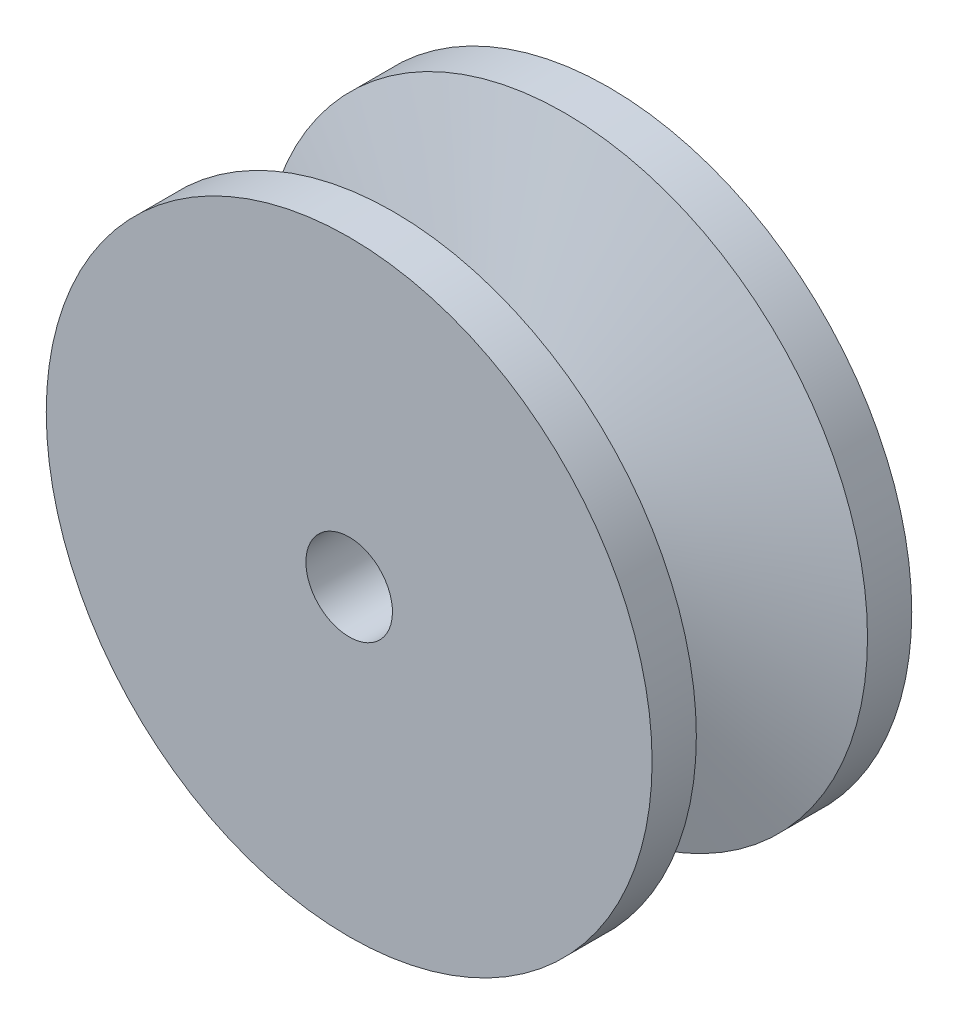
SolidWorks part; units mm, degrees
ref_plane "Front Plane" through (0, 0, 0) normal (0, 0, 1) x (1, 0, 0)
ref_plane "Top Plane" through (0, 0, 0) normal (0, 1, 0) x (1, 0, 0)
ref_plane "Right Plane" through (0, 0, 0) normal (1, 0, 0) x (0, 0, -1)
sketch "Sketch1" plane through (0, 0, 0) normal (1, 0, 0) x (0, 0, -1)
  line L0 (-9.525, 0) -> (9.525, 0) construction
  line L1 (-6.2793, 22.225) -> (6.2793, 22.225) construction
  line L2 (6.2793, 22.225) -> (9.525, 22.225)
  line L5 (-9.525, 22.225) -> (6.2793, 22.225) construction
  line L13 (-6.2793, 22.225) -> (-2.4742, 9.779)
  line L14 (-2.4742, 9.779) -> (2.4742, 9.779)
  line L15 (2.4742, 9.779) -> (6.2793, 22.225)
  line L16 (9.525, 3.175) -> (-9.525, 3.175) construction
  line L17 (0, 22.225) -> (0, 0) construction
  line L18 (-6.2793, 22.225) -> (-9.525, 22.225)
  line L22 (5.3086, 19.05) -> (-5.3086, 19.05) construction
  line L32 (-9.525, 0) -> (-9.525, 22.225)
  line L33 (9.525, 22.225) -> (9.525, 0)
  line L34 (-9.525, 0) -> (9.525, 0)
  point P16 (0, 9.779)
  dimension "A" = 34
  dimension "OD" = 44.45
  dimension "Bore" = 6.35
  dimension "Width" = 19.05
  dimension "PD" = 38.1
  dimension "W" = 19.05
  dimension "Depth" = 12.446
  dimension "bd" = 10.6172
  dimension "bg" = 12.5586
revolve "Revolve1" add sketch "Sketch1" angle 360 about L0
sketch "Sketch2" plane through (0, 0, -9.525) normal (0, 0, -1) x (-1, 0, 0)
  circle A0 centre (0, 0) radius 3.175
  circle A1 centre (0, 0) radius 19.05 construction
  point P4 (0, 3.175)
extrude "Cut-Extrude1" cut sketch "Sketch2" against normal up to vertex (19.05 mm away) up to point (0, 0, 9.525)
